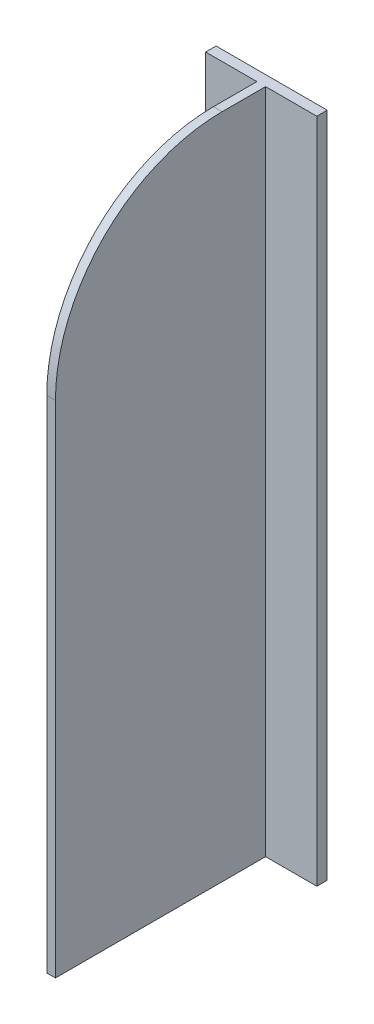
SolidWorks part; units mm, degrees
material "Plain Carbon Steel"
ref_plane "Front Plane" through (0, 0, 0) normal (0, 0, 1) x (1, 0, 0)
ref_plane "Top Plane" through (0, 0, 0) normal (0, 1, 0) x (1, 0, 0)
ref_plane "Right Plane" through (0, 0, 0) normal (1, 0, 0) x (0, 0, -1)
sketch "Sketch1" plane through (0, 0, 0) normal (0, 1, 0) x (-1, 0, 0)
  line L0 (-50.8, 0) -> (50.8, 0)
  line L1 (50.8, 0) -> (50.8, 9.525)
  line L2 (50.8, 9.525) -> (3.9687, 9.525)
  line L3 (3.9687, 9.525) -> (3.9688, 201.6125)
  line L4 (3.9688, 201.6125) -> (-3.9688, 201.6125)
  line L5 (-3.9688, 201.6125) -> (-3.9687, 9.525)
  line L6 (-3.9687, 9.525) -> (-50.8, 9.525)
  line L7 (-50.8, 9.525) -> (-50.8, 0)
  line L8 (-3.9687, 9.525) -> (3.9687, 9.525) construction
  dimension "D1" = 101.6
  dimension "D2" = 9.525
  dimension "D3" = 7.9375
  dimension "D4" = 201.6125
extrude "Boss-Extrude1" add sketch "Sketch1" along normal mid plane 609.6
sketch "Sketch2" plane through (0, -304.8, 0) normal (0, -1, 0) x (1, 0, 0)
  line L0 (0, 201.6125) -> (0, 0) construction
  line L1 (-3.9688, 201.6125) -> (3.9688, 201.6125) construction
sketch "Sketch3" plane through (0, 0, 0) normal (0, 0, -1) x (-1, 0, 0)
  line L0 (0, 304.8) -> (0, -304.8) construction
  line L1 (-50.8, 304.8) -> (50.8, 304.8) construction
  line L2 (-50.8, -304.8) -> (50.8, -304.8) construction
fillet "Fillet1" radius 152.4 1 edges at (0, 304.8, 201.6125)
sketch "Sketch4" plane through (0, 0, 201.6125) normal (0, 0, 1) x (1, 0, 0)
  line L0 (0, -304.8) -> (0, 152.4) construction
  line L1 (-3.9688, -304.8) -> (3.9688, -304.8) construction
  line L2 (3.9688, 152.4) -> (-3.9688, 152.4) construction
sketch "Sketch5" plane through (3.9687, 0, 0) normal (1, 0, 0) x (0, 0, -1)
  line L0 (-201.6125, -171.45) -> (-9.525, -171.45) construction
  line L1 (-201.6125, 152.4) -> (-201.6125, -304.8) construction
  line L2 (-9.525, 304.8) -> (-9.525, -304.8) construction
  line L3 (-201.6125, -12.7) -> (-9.525, -12.7) construction
  line L4 (-201.6125, 146.05) -> (-9.525, 146.05) construction
  line L5 (-201.6125, -304.8) -> (-9.525, -304.8) construction
  line L6 (-105.5688, -304.8) -> (-105.5688, 293.9971) construction
  arc A0 (-49.2125, 304.8) -> (-201.6125, 152.4) centre (-49.2125, 152.4) ccw construction
  dimension "D1" = 158.75
  dimension "D2" = 158.75
  dimension "D3" = 133.35
sketch "Sketch6" plane through (-3.9687, 0, 0) normal (-1, 0, 0) x (0, 0, 1)
  line L0 (9.525, 146.05) -> (201.6125, 146.05) construction
  line L1 (9.525, -12.7) -> (201.6125, -12.7) construction
  line L2 (9.525, -171.45) -> (201.6125, -171.45) construction
  line L3 (105.5688, -304.8) -> (105.5688, 293.9971) construction
